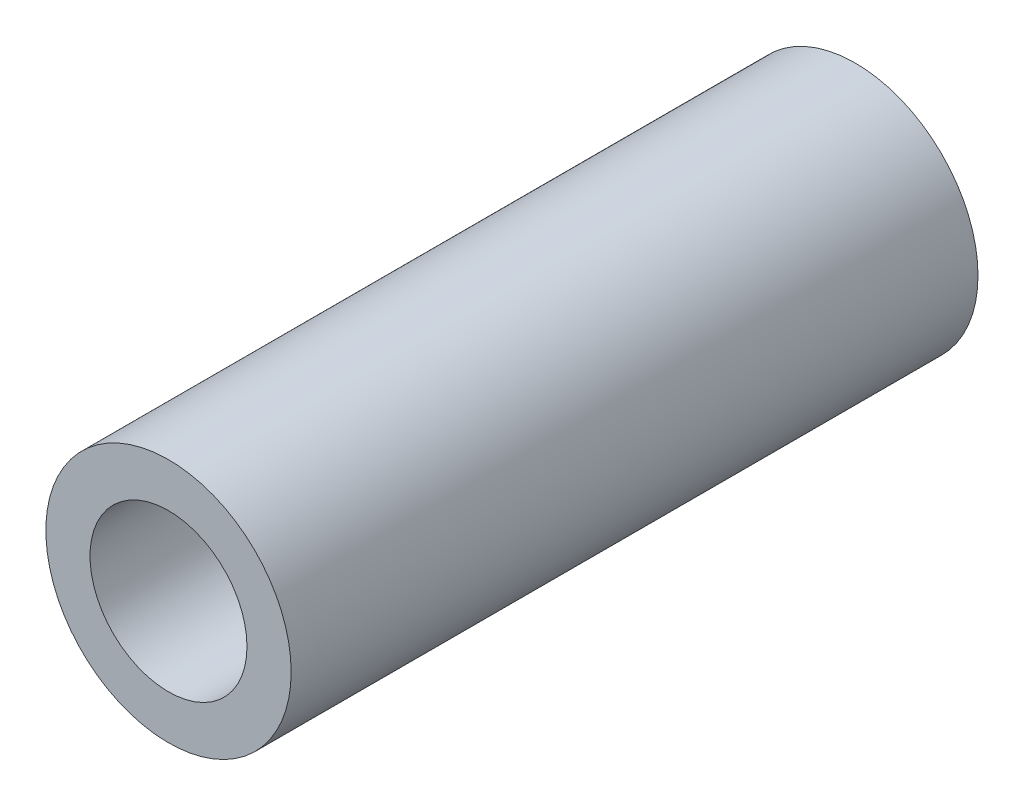
SolidWorks part; units mm, degrees
ref_plane "前视基准面" through (0, 0, 0) normal (0, 0, 1) x (1, 0, 0)
ref_plane "上视基准面" through (0, 0, 0) normal (0, 1, 0) x (1, 0, 0)
ref_plane "右视基准面" through (0, 0, 0) normal (1, 0, 0) x (0, 0, -1)
sketch "草图1" plane through (0, 0, 0) normal (0, 0, 1) x (1, 0, 0)
  circle A0 centre (0, 0) radius 1.6
  circle A1 centre (0, 0) radius 2.5
extrude "凸台-拉伸1" add sketch "草图1" along normal blind 14
